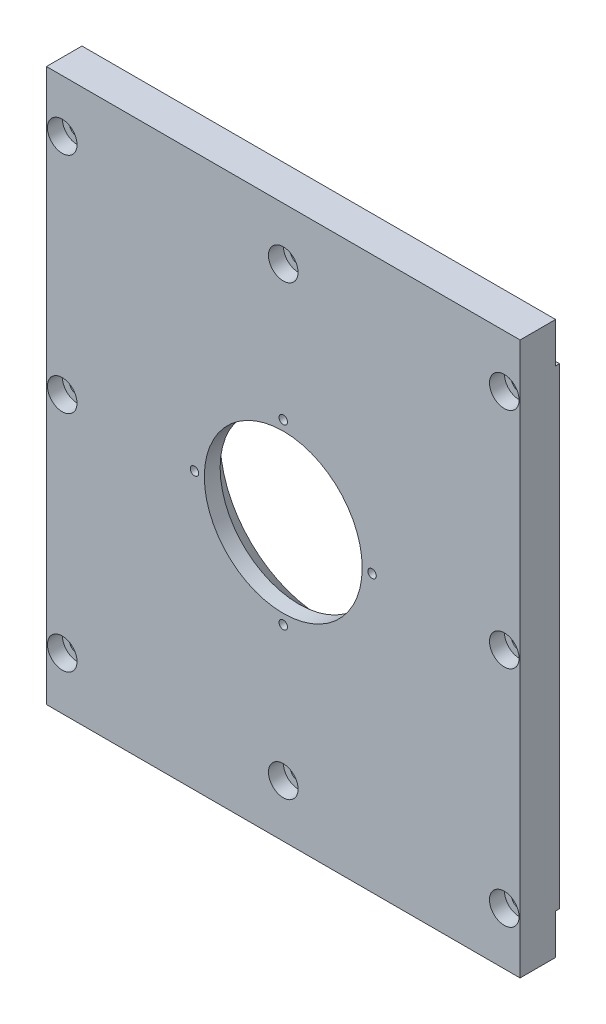
SolidWorks part; units mm, degrees
other "DetailItem1"
ref_plane "Front Plane" through (0, 0, 0) normal (0, 0, 1) x (1, 0, 0)
ref_plane "Top Plane" through (0, 0, 0) normal (0, 1, 0) x (1, 0, 0)
ref_plane "Right Plane" through (0, 0, 0) normal (1, 0, 0) x (0, 0, -1)
sketch "Sketch1" plane through (0, 0, 0) normal (0, 0, 1) x (1, 0, 0)
  line L1 (-76.2, 88.9) -> (76.2, 88.9)
  line L2 (-76.2, 88.9) -> (-76.2, -88.9)
  line L3 (-76.2, -88.9) -> (76.2, -88.9)
  line L4 (76.2, 88.9) -> (76.2, -88.9)
  dimension "D1" = 152.4
  dimension "D2" = 177.8
  dimension "D3" = 88.9
  dimension "D4" = 76.2
extrude "Boss-Extrude1" add sketch "Sketch1" along normal blind 12.7
sketch "Sketch2" plane through (0, 0, 12.7) normal (0, 0, 1) x (1, 0, 0)
  line L0 (-76.2, 88.9) -> (-76.2, -88.9) construction
  line L1 (-25.4, 38.1) -> (25.4, 38.1)
  line L2 (-25.4, 38.1) -> (-25.4, -38.1)
  line L3 (-25.4, -38.1) -> (25.4, -38.1)
  line L4 (25.4, 38.1) -> (25.4, -38.1)
  line L5 (76.2, 88.9) -> (-76.2, 88.9) construction
  line L6 (76.2, -88.9) -> (76.2, 88.9) construction
  line L7 (-76.2, -88.9) -> (76.2, -88.9) construction
  dimension "D1" = 50.8
  dimension "D2" = 50.8
  dimension "D3" = 50.8
  dimension "D4" = 50.8
extrude "Cut-Extrude1" [suppressed] cut sketch "Sketch2" against normal through all
sketch "Sketch3" plane through (0, 0, 0) normal (0, 0, -1) x (-1, 0, 0)
  circle A0 centre (0, 0) radius 25.4
  dimension "D1" = 50.8
extrude "Cut-Extrude2" cut sketch "Sketch3" against normal through all
hole_wizard "#4-40 Tapped Hole1" [suppressed] positions "Sketch5" profile "Sketch4" tap size "#4-40" standard "ANSI Inch"
sketch "Sketch5" plane through (0, 0, 12.7) normal (0, 0, 1) x (1, 0, 0)
  line L0 (0, 0) -> (-66.9762, 0) construction
  line L3 (0, 0) -> (-48.0849, 48.0849) construction
  point P0 (-31.75, 31.75)
  dimension "D1" = 44.9013
  dimension "D2" = 45
sketch "Sketch4" plane through (-31.75, 31.75, 12.7) normal (1, 0, 0) x (0, -1, 0)
  line L0 (0, 0) -> (0, 10.8392)
  line L1 (0, 10.8392) -> (1.1303, 10.16)
  line L2 (1.1303, 10.16) -> (1.1303, 0)
  line L5 (1.1303, 0) -> (0, 0)
  line L10 (0, 10.8392) -> (-1.1303, 10.16) construction
  line L11 (0, -6.35) -> (0, 107.95) construction
  dimension "Tap Drill Dia." = 2.2606
  dimension "Tap Drill Depth" = 10.16
  dimension "Drill Angle" = 118
sketch "Sketch6" [suppressed] plane through (0, 0, 12.7) normal (0, 0, 1) x (1, 0, 0)
  circle A0 centre (-31.75, 31.75) radius 3.302
  dimension "D1" = 6.604
extrude "Cut-Extrude3" [suppressed] cut sketch "Sketch6" against normal blind 3.175
pattern_circular "CirPattern1" [suppressed] count 4 over 360
mirror "Mirror1" [suppressed] about plane through (0, 0, 0) normal (1, 0, 0)
mirror "Mirror2" [suppressed] about plane through (0, 0, 0) normal (0, 1, 0)
hole_wizard "CBORE for #10 Socket Head Cap Screw1" [suppressed] positions "Sketch8" profile "Sketch7" counterbore size "#10" standard "ANSI Inch"
sketch "Sketch8" plane through (0, 0, 0) normal (0, 0, -1) x (-1, 0, 0)
  line L0 (-76.2, -76.2) -> (-76.2, 76.2) construction
  point P0 (-25.4, 72.009)
  point P2 (-25.4, -72.009)
  point P9 (-71.4375, 0)
  dimension "D1" = 144.018
  dimension "D2" = 50.8
  dimension "D3" = 72.009
  dimension "D4" = 50.8
  dimension "D5" = 71.4375
sketch "Sketch7" plane through (25.4, 72.009, 0) normal (1, 0, 0) x (0, 1, 0)
  line L0 (0, 0) -> (0, 12.7)
  line L1 (0, 12.7) -> (1.5875, 12.7)
  line L3 (1.5875, 12.7) -> (1.5875, 6.35)
  line L4 (1.5875, 6.35) -> (3.175, 6.35)
  line L5 (3.175, 6.35) -> (3.175, 0)
  line L7 (3.175, 0) -> (0, 0)
  line L11 (0, -6.35) -> (0, 107.95) construction
  dimension "Thru Hole Dia." = 3.175
  dimension "Thru Hole Depth" = 12.7
  dimension "C'Bore Dia." = 6.35
  dimension "C'Bore Depth" = 6.35
mirror "Mirror3" [suppressed] about plane through (0, 0, 0) normal (1, 0, 0)
hole_wizard "CBORE for #10 Socket Head Cap Screw2" positions "Sketch10" profile "Sketch9" counterbore size "#10" standard "ANSI Inch" end condition through all
sketch "Sketch10" plane through (0, 0, 12.7) normal (0, 0, 1) x (1, 0, 0)
  line L0 (76.2, -88.9) -> (76.2, 88.9) construction
  line L1 (76.2, 88.9) -> (-76.2, 88.9) construction
  line L2 (76.2, -88.9) -> (76.2, 88.9) construction
  point P0 (71.12, 72.009)
  point P8 (0, 72.009)
  point P13 (71.12, 0)
  dimension "D1" = 5.08
  dimension "D2" = 16.891
  dimension "D3" = 16.891
  dimension "D4" = 5.08
sketch "Sketch9" plane through (71.12, 72.009, 12.7) normal (1, 0, 0) x (0, -1, 0)
  line L0 (0, 0) -> (0, 12.7)
  line L1 (0, 12.7) -> (2.5527, 12.7)
  line L3 (2.5527, 12.7) -> (2.5527, 4.826)
  line L4 (2.5527, 4.826) -> (4.7625, 4.826)
  line L5 (4.7625, 4.826) -> (4.7625, 0)
  line L7 (4.7625, 0) -> (0, 0)
  line L11 (0, -6.35) -> (0, 107.95) construction
  dimension "Thru Hole Dia." = 5.1054
  dimension "Thru Hole Depth" = 12.7
  dimension "C'Bore Dia." = 9.525
  dimension "C'Bore Depth" = 4.826
mirror "Mirror4" about plane through (0, 0, 0) normal (0, 1, 0) of "CBORE for #10 Socket Head Cap Screw2"
mirror "Mirror5" about plane through (0, 0, 0) normal (1, 0, 0) of "Mirror4", "CBORE for #10 Socket Head Cap Screw2"
sketch "Sketch11" plane through (0, 0, 12.7) normal (0, 0, 1) x (1, 0, 0)
  line L1 (-38.1, 38.1) -> (38.1, 38.1)
  line L2 (-38.1, 38.1) -> (-38.1, -38.1)
  line L3 (-38.1, -38.1) -> (38.1, -38.1)
  line L4 (38.1, 38.1) -> (38.1, -38.1)
  dimension "D1" = 76.2
  dimension "D2" = 38.1
  dimension "D3" = 76.2
  dimension "D4" = 38.1
extrude "Cut-Extrude4" [suppressed] cut sketch "Sketch11" against normal blind 3.175
fillet "Fillet1" [suppressed] radius 3.175
pattern_circular "CirPattern2" [suppressed] count 4 over 360
hole_wizard "#4-40 Tapped Hole3" [suppressed] positions "Sketch15" profile "Sketch17" tap size "#4-40" standard "ANSI Inch"
sketch "Sketch15" plane through (-62.1409, 22.4504, 0) normal (0, 0, -1) x (-1, 0, 0)
  line L3 (-62.1409, -22.4504) -> (-62.1409, 36.5893) construction
  point P0 (-62.1409, 22.4568)
  dimension "D1" = 44.9072
sketch "Sketch17" plane through (0, 44.9072, 0) normal (1, 0, 0) x (0, 1, 0)
  line L0 (0, 0) -> (0, 10.8392)
  line L1 (0, 10.8392) -> (1.1303, 10.16)
  line L2 (1.1303, 10.16) -> (1.1303, 0)
  line L5 (1.1303, 0) -> (0, 0)
  line L10 (0, 10.8392) -> (-1.1303, 10.16) construction
  line L11 (0, -6.35) -> (0, 107.95) construction
  dimension "Tap Drill Dia." = 2.2606
  dimension "Tap Drill Depth" = 10.16
  dimension "Drill Angle" = 118
sketch "Sketch19" [suppressed] plane through (-62.1409, 22.4504, 0) normal (0, 0, -1) x (-1, 0, 0)
  circle A0 centre (-62.1409, 22.4568) radius 3.302
  dimension "D1" = 6.604
extrude "Cut-Extrude5" [suppressed] cut sketch "Sketch19" against normal blind 3.175
pattern_circular "CirPattern3" [suppressed] count 4 over 360
sketch "Sketch20" [suppressed] plane through (0, 0, 12.7) normal (0, 0, 1) x (1, 0, 0)
  circle A0 centre (-31.75, 31.75) radius 6.604
  dimension "D1" = 13.208
extrude "Cut-Extrude6" [suppressed] cut sketch "Sketch20" against normal blind 6.35
mirror "Mirror6" [suppressed] about plane through (0, 0, 0) normal (1, 0, 0)
mirror "Mirror7" [suppressed] about plane through (0, 0, 0) normal (0, 1, 0)
sketch "Sketch21" plane through (0, 0, 0) normal (0, 0, -1) x (-1, 0, 0)
  line L1 (-88.9, 94.996) -> (88.9, 94.996)
  line L2 (-88.9, 94.996) -> (-88.9, 75.946)
  line L3 (-88.9, 75.946) -> (88.9, 75.946)
  line L4 (88.9, 94.996) -> (88.9, 75.946)
  line L5 (-76.2, 88.9) -> (76.2, 88.9) construction
  dimension "D1" = 12.954
  dimension "D2" = 177.8
  dimension "D3" = 88.9
  dimension "D4" = 19.05
extrude "Cut-Extrude7" cut sketch "Sketch21" against normal blind 1.27
mirror "Mirror8" about plane through (0, 0, 0) normal (0, 1, 0) of "Cut-Extrude7"
sketch "Sketch22" plane through (0, 0, 0) normal (0, 0, -1) x (-1, 0, 0)
  line L0 (0, 0) -> (50.4411, 0) construction
  line L1 (0, 0) -> (40.8884, 40.8884) construction
  circle A0 centre (31.75, 31.75) radius 6.604
  dimension "D1" = 13.208
  dimension "D2" = 44.9013
  dimension "D3" = 45
extrude "Cut-Extrude8" cut sketch "Sketch22" against normal blind 8.89
pattern_circular "CirPattern4" count 4 over 360 about axis through (0, 0, 0) along (0, 0, 1) of "Cut-Extrude8"
hole_wizard "#6-32 Tapped Hole1" positions "Sketch25" profile "Sketch24" tap size "#6-32" standard "ANSI Inch"
sketch "Sketch25" plane through (0, 0, 12.7) normal (0, 0, 1) x (1, 0, 0)
  point P0 (0, 28.575)
  dimension "D1" = 28.575
sketch "Sketch24" plane through (0, 28.575, 12.7) normal (1, 0, 0) x (0, -1, 0)
  line L0 (0, 0) -> (0, 5.8927)
  line L1 (0, 5.8927) -> (1.3525, 5.08)
  line L2 (1.3525, 5.08) -> (1.3525, 0)
  line L5 (1.3525, 0) -> (0, 0)
  line L10 (0, 5.8927) -> (-1.3526, 5.08) construction
  line L11 (0, -6.35) -> (0, 107.95) construction
  dimension "Tap Drill Dia." = 2.7051
  dimension "Tap Drill Depth" = 5.08
  dimension "Drill Angle" = 118
sketch "Sketch26" plane through (0, 0, 12.7) normal (0, 0, 1) x (1, 0, 0)
  circle A0 centre (0, 28.575) radius 3.302
  dimension "D1" = 6.604
extrude "Cut-Extrude9" [suppressed] cut sketch "Sketch26" against normal blind 3.175
pattern_circular "CirPattern5" count 4 over 360 about axis through (0, 0, 0) along (0, 0, 1) of "#6-32 Tapped Hole1", "Cut-Extrude9"
sketch "Sketch27" plane through (0, 0, 0) normal (0, 0, 1) x (1, 0, 0)
  line L1 (-50.1142, 52.6542) -> (50.1142, 52.6542)
  line L2 (-52.6542, 50.1142) -> (-52.6542, -50.1142)
  line L3 (-50.1142, -52.6542) -> (50.1142, -52.6542)
  line L4 (52.6542, 50.1142) -> (52.6542, -50.1142)
  line L8 (-50.1142, 54.991) -> (50.1142, 54.991)
  line L9 (54.991, 50.1142) -> (54.991, -50.1142)
  line L10 (-50.1142, -54.991) -> (50.1142, -54.991)
  line L11 (-54.991, 50.1142) -> (-54.991, -50.1142)
  arc A0 (-52.6542, -50.1142) -> (-50.1142, -52.6542) centre (-50.1142, -50.1142) ccw
  arc A1 (50.1142, -52.6542) -> (52.6542, -50.1142) centre (50.1142, -50.1142) ccw
  arc A2 (50.1142, 52.6542) -> (52.6542, 50.1142) centre (50.1142, 50.1142) cw
  arc A3 (-50.1142, 52.6542) -> (-52.6542, 50.1142) centre (-50.1142, 50.1142) ccw
  arc A4 (50.1142, 54.991) -> (54.991, 50.1142) centre (50.1142, 50.1142) cw
  arc A5 (50.1142, -54.991) -> (54.991, -50.1142) centre (50.1142, -50.1142) ccw
  arc A6 (-54.991, -50.1142) -> (-50.1142, -54.991) centre (-50.1142, -50.1142) ccw
  arc A7 (-50.1142, 54.991) -> (-54.991, 50.1142) centre (-50.1142, 50.1142) ccw
  dimension "D6" = 2.54
  dimension "D1" = 109.982
  dimension "D2" = 109.982
  dimension "D3" = 54.991
  dimension "D4" = 54.991
  dimension "D5" = 2.3368
extrude "Cut-Extrude14" [suppressed] cut sketch "Sketch27" along normal blind 2.032
chamfer "Chamfer1" distance 7.62 angle 45 1 edges at (-25.4, 0, 0)
sketch "Sketch28" plane through (0, 0, 0) normal (0, 0, 1) x (1, 0, 0)
  line L1 (-62.7507, 65.2907) -> (62.7507, 65.2907)
  line L2 (-65.2907, 62.7507) -> (-65.2907, -62.7507)
  line L3 (-62.7507, -65.2907) -> (62.7507, -65.2907)
  line L4 (65.2907, 62.7507) -> (65.2907, -62.7507)
  line L8 (-62.7507, 67.6275) -> (62.7507, 67.6275)
  line L9 (67.6275, 62.7507) -> (67.6275, -62.7507)
  line L10 (-62.7507, -67.6275) -> (62.7507, -67.6275)
  line L11 (-67.6275, 62.7507) -> (-67.6275, -62.7507)
  arc A0 (-65.2907, -62.7507) -> (-62.7507, -65.2907) centre (-62.7507, -62.7507) ccw
  arc A1 (62.7507, -65.2907) -> (65.2907, -62.7507) centre (62.7507, -62.7507) ccw
  arc A2 (62.7507, 65.2907) -> (65.2907, 62.7507) centre (62.7507, 62.7507) cw
  arc A3 (-62.7507, 65.2907) -> (-65.2907, 62.7507) centre (-62.7507, 62.7507) ccw
  arc A4 (62.7507, 67.6275) -> (67.6275, 62.7507) centre (62.7507, 62.7507) cw
  arc A5 (62.7507, -67.6275) -> (67.6275, -62.7507) centre (62.7507, -62.7507) ccw
  arc A6 (-67.6275, -62.7507) -> (-62.7507, -67.6275) centre (-62.7507, -62.7507) ccw
  arc A7 (-62.7507, 67.6275) -> (-67.6275, 62.7507) centre (-62.7507, 62.7507) ccw
  dimension "D6" = 2.54
  dimension "D1" = 135.255
  dimension "D2" = 135.255
  dimension "D3" = 67.6275
  dimension "D4" = 67.6275
  dimension "D5" = 2.3368
extrude "Cut-Extrude15" cut sketch "Sketch28" along normal blind 2.032
equation "\"D3@Sketch1\"=\"D2@Sketch1\"/2"
equation "\"D4@Sketch1\"=\"D1@Sketch1\"/2"
equation "\"D2@Sketch2\"=\"D1@Sketch2\""
equation "\"D3@Sketch2\"=\"D1@Sketch2\""
equation "\"D4@Sketch2\"=\"D1@Sketch2\""
equation "\"D3@Sketch8\"=\"D1@Sketch8\"/2"
equation "\"D2@Sketch11\"=\"D1@Sketch11\"/2"
equation "\"D4@Sketch11\"=\"D3@Sketch11\"/2"
equation "\"D1@Sketch5\"=1.25/(sin(45))"
equation "\"D2@Sketch8\"=\"D4@Sketch8\""
equation "\"D3@Sketch21\"=\"D2@Sketch21\"/2"
equation "\"D2@Sketch22\"=1.25/(sin(45))"
equation "\"D3@Sketch27\"=\"D1@Sketch27\"/2"
equation "\"D4@Sketch27\"=\"D2@Sketch27\"/2"
equation "\"D2@Sketch27\"=\"D1@Sketch27\""
equation "\"D2@Sketch10\"=\"D3@Sketch10\""
equation "\"D3@Sketch28\"=\"D1@Sketch28\"/2"
equation "\"D4@Sketch28\"=\"D2@Sketch28\"/2"
